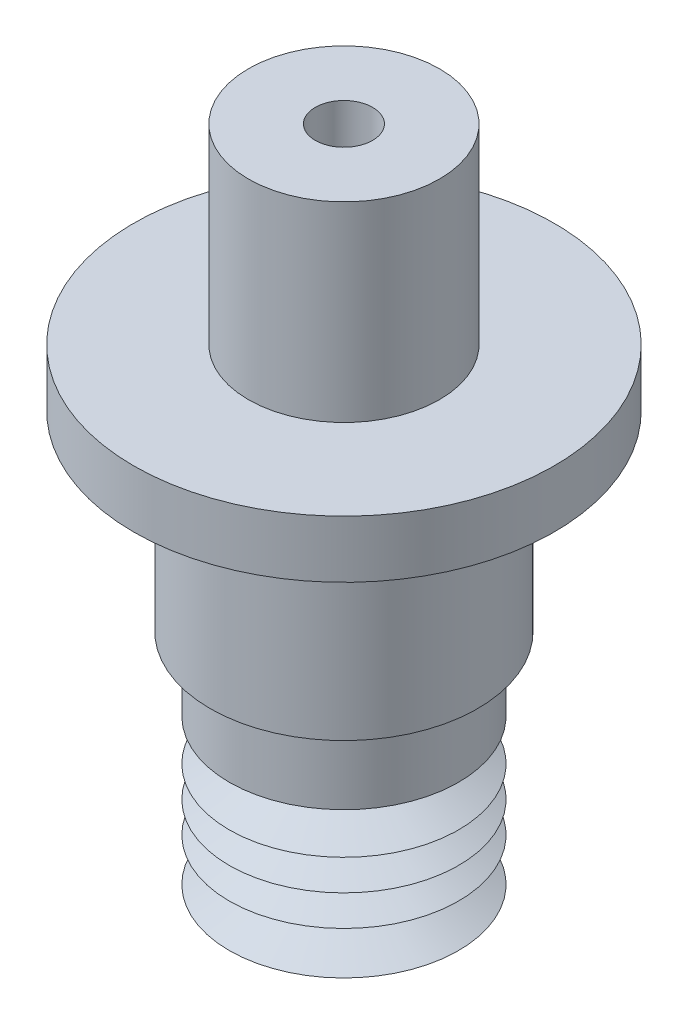
SolidWorks part; units mm, degrees
ref_plane "前视基准面" through (0, 0, 0) normal (0, 0, 1) x (1, 0, 0)
ref_plane "上视基准面" through (0, 0, 0) normal (0, 1, 0) x (1, 0, 0)
ref_plane "右视基准面" through (0, 0, 0) normal (1, 0, 0) x (0, 0, -1)
ref_plane "基准面4" through (0, 0, 0) normal (0, 0, -1) x (-1, 0, 0)
sketch "草图1" plane through (0, 0, 0) normal (0, 0, -1) x (-1, 0, 0)
  line L0 (-6, -4) -> (-3.7056, -4)
  line L1 (-3.7056, -4) -> (-2.0601, -3.2031)
  line L2 (-2.0601, -3.2031) -> (-3.9986, -1.898)
  line L3 (-3.9986, -1.898) -> (-1.4527, -0.6651)
  line L4 (-1.4527, -0.6651) -> (-3.3913, 0.0085)
  line L5 (-3.3913, 0.0085) -> (-1.4527, 0.9472)
  line L6 (-1.4527, 0.9472) -> (-3.3913, 1.6208)
  line L7 (-3.3913, 1.6208) -> (-2.0014, 2.2939)
  line L8 (-2.0014, 2.2939) -> (-5, 4.1783)
  line L9 (-5, 4.1783) -> (-5, 6.4651)
  line L10 (-5, 6.4651) -> (-2, 6.4651)
  line L11 (-2, 7.4651) -> (-2, 6.4651)
  line L12 (-2, 7.4651) -> (-6, 7.4651)
  line L13 (-6, 7.4651) -> (-6, 3.6257)
  line L14 (-6, 3.6257) -> (-4.0614, 2.4074)
  line L15 (-4.0614, 2.4074) -> (-6, 1.4686)
  line L16 (-6, 1.4686) -> (-4.0614, 0.795)
  line L17 (-4.0614, 0.795) -> (-6, -0.1437)
  line L18 (-6, -0.1437) -> (-4.0614, -0.8173)
  line L19 (-4.0614, -0.8173) -> (-6, -1.7561)
  line L20 (-6, -1.7561) -> (-4.0614, -3.0612)
  line L21 (-4.0614, -3.0612) -> (-6, -4)
  line L22 (0, -4) -> (0, 7.4651) construction
revolve "旋转1" add sketch "草图1" angle 360 about L22
sketch "草图2" plane through (0, 7.4651, 0) normal (0, 1, 0) x (1, 0, 0)
  circle A0 centre (0, 0) radius 7
extrude "凸台-拉伸1" add sketch "草图2" along normal blind 10
sketch "草图3" plane through (0, 17.4651, 0) normal (0, 1, 0) x (1, 0, 0)
  circle A0 centre (0, 0) radius 11
extrude "凸台-拉伸2" add sketch "草图3" along normal blind 3
sketch "草图4" plane through (0, 20.4651, 0) normal (0, 1, 0) x (1, 0, 0)
  circle A0 centre (0, 0) radius 5
  circle A1 centre (0, 0) radius 1.5
extrude "凸台-拉伸3" add sketch "草图4" along normal blind 10
